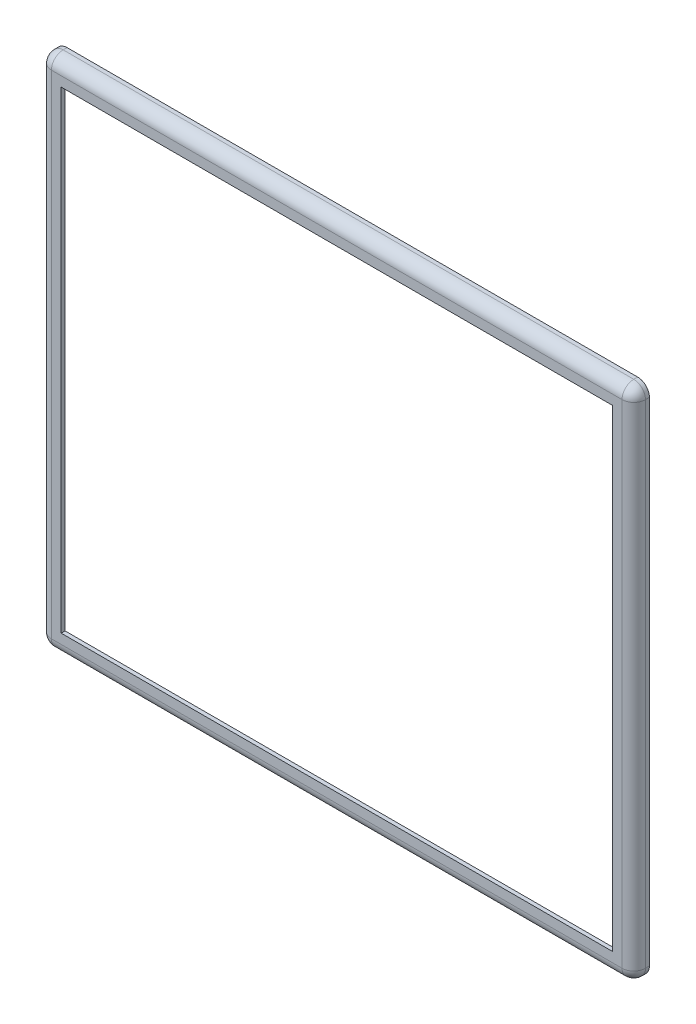
SolidWorks part; units mm, degrees
ref_plane "Front Plane" through (0, 0, 0) normal (0, 0, 1) x (1, 0, 0)
ref_plane "Top Plane" through (0, 0, 0) normal (0, 1, 0) x (1, 0, 0)
ref_plane "Right Plane" through (0, 0, 0) normal (1, 0, 0) x (0, 0, -1)
sketch "Sketch1" plane through (0, 0, 0) normal (0, 0, 1) x (1, 0, 0)
  line L1 (-75.3794, 57.0333) -> (74.6206, 57.0333)
  line L2 (-75.3794, 57.0333) -> (-75.3794, -72.9667)
  line L3 (-75.3794, -72.9667) -> (74.6206, -72.9667)
  line L4 (74.6206, 57.0333) -> (74.6206, -72.9667)
  line L5 (-76.3794, 58.0333) -> (75.6206, 58.0333)
  line L6 (-76.3794, 58.0333) -> (-76.3794, -73.9667)
  line L7 (-76.3794, -73.9667) -> (75.6206, -73.9667)
  line L8 (75.6206, 58.0333) -> (75.6206, -73.9667)
  dimension "D1" = 150
  dimension "D2" = 130
  dimension "D3" = 1
  dimension "D4" = 1
  dimension "D5" = 1
  dimension "D6" = 1
extrude "Boss-Extrude1" add sketch "Sketch1" along normal blind 3
sketch "Sketch2" plane through (0, 0, 3) normal (0, 0, 1) x (1, 0, 0)
  line L0 (74.6206, -72.9667) -> (74.6206, 57.0333) construction
  line L1 (-76.3794, 58.0333) -> (75.6206, 58.0333)
  line L2 (-76.3794, 58.0333) -> (-76.3794, -73.9667)
  line L3 (-76.3794, -73.9667) -> (75.6206, -73.9667)
  line L4 (75.6206, 58.0333) -> (75.6206, -73.9667)
  line L5 (-70.8794, 52.5333) -> (70.1206, 52.5333)
  line L6 (-70.8794, 52.5333) -> (-70.8794, -68.4667)
  line L7 (-70.8794, -68.4667) -> (70.1206, -68.4667)
  line L8 (70.1206, 52.5333) -> (70.1206, -68.4667)
  line L9 (-75.3794, -72.9667) -> (74.6206, -72.9667) construction
  line L10 (-75.3794, 57.0333) -> (-75.3794, -72.9667) construction
  line L11 (74.6206, 57.0333) -> (-75.3794, 57.0333) construction
  dimension "D1" = 4.5
  dimension "D2" = 4.5
  dimension "D3" = 4.5
  dimension "D4" = 4.5
extrude "Boss-Extrude2" add sketch "Sketch2" along normal blind 1
fillet "Fillet1" radius 1.4 8 edges at (74.6206, -7.9667, 3) (-0.3794, 57.0333, 3) (-75.3794, -7.9667, 3) (-0.3794, -72.9667, 3) (74.6206, 57.0333, 1.5) (-75.3794, 57.0333, 1.5) (-75.3794, -72.9667, 1.5) (74.6206, -72.9667, 1.5)
fillet "Fillet2" radius 3 8 edges at (75.6206, -7.9667, 4) (-0.3794, 58.0333, 4) (-76.3794, -7.9667, 4) (-0.3794, -73.9667, 4) (75.6206, -73.9667, 2) (75.6206, 58.0333, 2) (-76.3794, 58.0333, 2) (-76.3794, -73.9667, 2)
